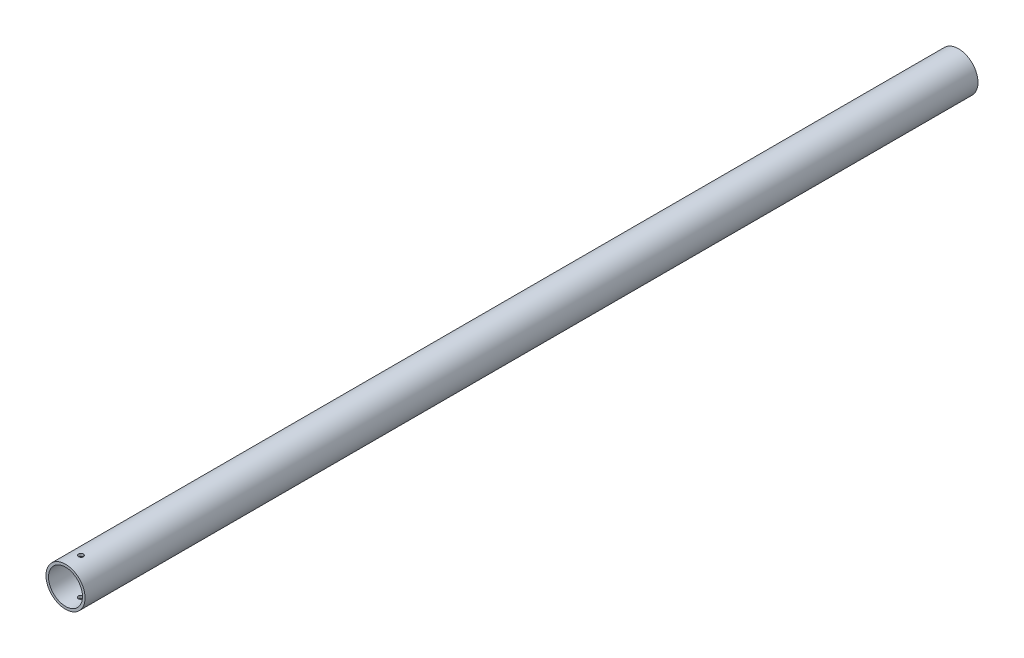
SolidWorks part; units mm, degrees
material "6063-T6, Rod (SS)"
ref_plane "Front Plane" through (0, 0, 0) normal (0, 0, 1) x (1, 0, 0)
ref_plane "Top Plane" through (0, 0, 0) normal (0, 1, 0) x (1, 0, 0)
ref_plane "Right Plane" through (0, 0, 0) normal (1, 0, 0) x (0, 0, -1)
sketch "Sketch1" plane through (0, 0, 0) normal (0, 0, 1) x (1, 0, 0)
  circle A0 centre (0, 0) radius 12.7
  circle A1 centre (0, 0) radius 11.049
  dimension "D1" = 25.4
  dimension "D2" = 22.098
extrude "Boss-Extrude1" add sketch "Sketch1" along normal blind 580
sketch "Sketch2" plane through (0, 0, 0) normal (0, 1, 0) x (1, 0, 0)
  line L0 (-12.7, -580) -> (12.7, -580) construction
  line L1 (-12.7, -570) -> (12.7, -570) construction
  line L2 (-12.7, 0) -> (-12.7, -580) construction
  line L3 (12.7, -580) -> (12.7, 0) construction
  circle A0 centre (0, -570) radius 1.6
  point P10 (0, -590)
  point P11 (0, -590)
  dimension "D1" = 3.2
  dimension "D2" = 10
extrude "Cut-Extrude1" cut sketch "Sketch2" against normal through all both and the other way through all
